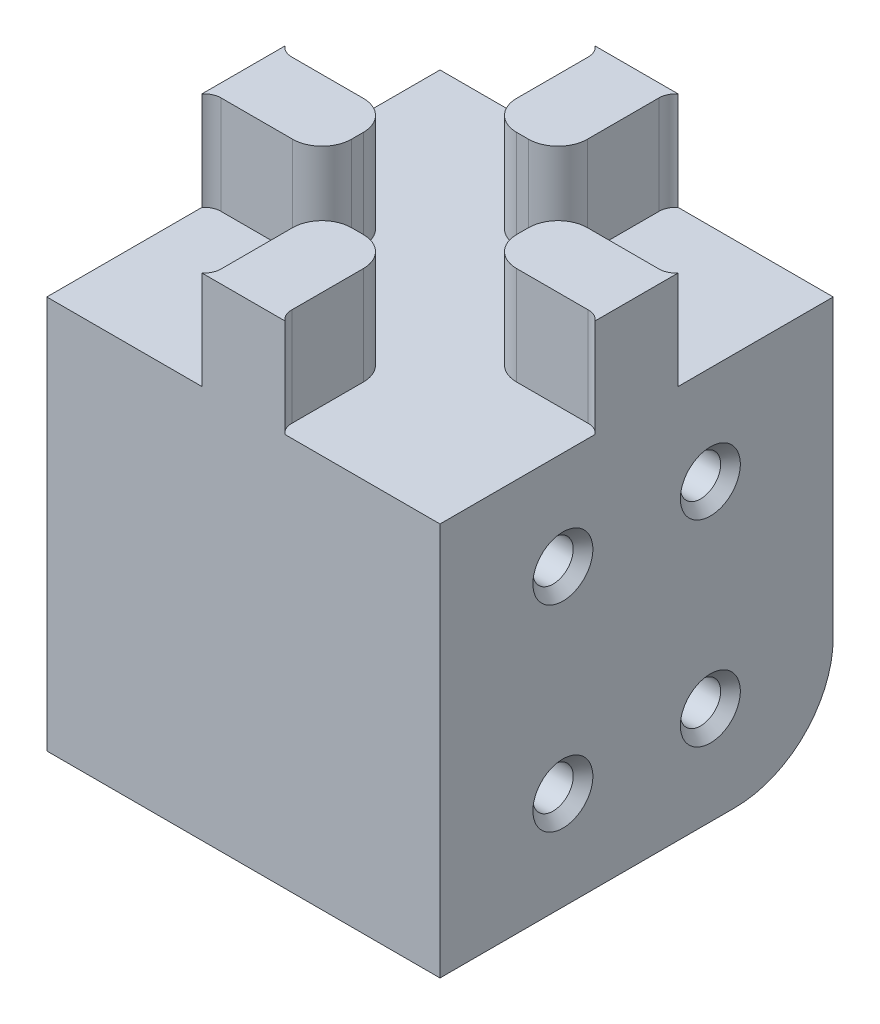
SolidWorks part; units mm, degrees
material "ABS"
ref_plane "Front Plane" through (0, 0, 0) normal (0, 0, 1) x (1, 0, 0)
ref_plane "Top Plane" through (0, 0, 0) normal (0, 1, 0) x (1, 0, 0)
ref_plane "Right Plane" through (0, 0, 0) normal (1, 0, 0) x (0, 0, -1)
sketch "Sketch1" plane through (0, 0, 0) normal (0, 1, 0) x (1, 0, 0)
  line L1 (-20, -20) -> (20, -20)
  line L2 (-20, -20) -> (-20, 20)
  line L3 (-20, 20) -> (20, 20)
  line L4 (20, -20) -> (20, 20)
  line L5 (-20, -20) -> (20, 20) construction
  line L6 (-20, 20) -> (20, -20) construction
  point P0 (0, 0)
  dimension "D1" = 40
  dimension "D2" = 40
extrude "Boss-Extrude1" add sketch "Sketch1" along normal mid plane 40 contours L3 L4 L1 L2
sketch "Sketch2" plane through (0, 0, 0) normal (1, 0, 0) x (0, 0, -1)
  line B0 (-7.5, -10) -> (-7.5, 10) construction
  line B1 (7.5, -10) -> (7.5, 10) construction
  circle B2 centre (-7.5, 10) radius 2.05
  circle B3 centre (7.5, 10) radius 2.05
  circle B4 centre (-7.5, -10) radius 2.05
  circle B5 centre (7.5, -10) radius 2.05
sketch_block_instance "Block1-1"
sketch_block "Block1" parameters "D1"=4.1, "D2"=20, "D3"=15
extrude "Cut-Extrude1" cut sketch "Sketch2" against normal through all from offset 13
mirror "Mirror1" about plane through (0, 0, 0) normal (1, 0, 0) of "Cut-Extrude1"
sketch "Sketch3" plane through (0, 20, 0) normal (0, 1, 0) x (1, 0, 0)
  line L0 (11.8267, 9.3942) -> (11.8267, 9.4899)
  line L1 (11.8267, 9.4899) -> (11.9223, 9.4899)
  line L2 (11.9223, 9.4899) -> (12.39, 9.9576)
  line L3 (12.39, 9.9576) -> (12.39, 10.0532)
  line L4 (12.39, 10.0532) -> (12.4857, 10.0532)
  line L5 (12.4857, 10.0532) -> (12.9739, 10.5414)
  line L6 (13.1153, 10.6) -> (16.76, 10.6)
  line L7 (16.96, 10.4) -> (16.96, 7.15)
  line L8 (16.96, 7.15) -> (16.3, 7.15)
  line L9 (16.3, 7.15) -> (16.3, 5.32)
  line L10 (18.02, 3.6) -> (18.68, 3.6)
  line L11 (20.4, 5.32) -> (20.4, 17)
  line L12 (17, 20.4) -> (5.32, 20.4)
  line L13 (3.6, 18.68) -> (3.6, 18.02)
  line L14 (5.32, 16.3) -> (7.15, 16.3)
  line L15 (7.15, 16.3) -> (7.15, 16.96)
  line L16 (7.15, 16.96) -> (10.4, 16.96)
  line L17 (10.6, 16.76) -> (10.6, 13.1153)
  line L18 (10.5414, 12.9739) -> (6.237, 8.6695)
  line L19 (5.5865, 8.4) -> (-5.5865, 8.4)
  line L20 (-6.237, 8.6695) -> (-10.5414, 12.9739)
  line L21 (-10.6, 13.1153) -> (-10.6, 16.76)
  line L22 (-10.4, 16.96) -> (-7.15, 16.96)
  line L23 (-7.15, 16.96) -> (-7.15, 16.3)
  line L24 (-7.15, 16.3) -> (-5.32, 16.3)
  line L25 (-3.6, 18.02) -> (-3.6, 18.68)
  line L26 (-5.32, 20.4) -> (-17, 20.4)
  line L27 (-20.4, 17) -> (-20.4, 5.32)
  line L28 (-18.68, 3.6) -> (-18.02, 3.6)
  line L29 (-16.3, 5.32) -> (-16.3, 7.15)
  line L30 (-16.3, 7.15) -> (-16.96, 7.15)
  line L31 (-16.96, 7.15) -> (-16.96, 10.4)
  line L32 (-16.76, 10.6) -> (-13.1153, 10.6)
  line L33 (-12.9739, 10.5414) -> (-8.6695, 6.237)
  line L34 (-8.4, 5.5865) -> (-8.4, -5.5865)
  line L35 (-8.6695, -6.237) -> (-12.9739, -10.5414)
  line L36 (-13.1153, -10.6) -> (-16.76, -10.6)
  line L37 (-16.96, -10.4) -> (-16.96, -7.15)
  line L38 (-16.96, -7.15) -> (-16.3, -7.15)
  line L39 (-16.3, -7.15) -> (-16.3, -5.32)
  line L40 (-18.02, -3.6) -> (-18.68, -3.6)
  line L41 (-20.4, -5.32) -> (-20.4, -17)
  line L42 (-17, -20.4) -> (-5.32, -20.4)
  line L43 (-3.6, -18.68) -> (-3.6, -18.02)
  line L44 (-5.32, -16.3) -> (-7.15, -16.3)
  line L45 (-7.15, -16.3) -> (-7.15, -16.96)
  line L46 (-7.15, -16.96) -> (-10.4, -16.96)
  line L47 (-10.6, -16.76) -> (-10.6, -13.1153)
  line L48 (-10.5414, -12.9739) -> (-6.237, -8.6695)
  line L49 (-5.5865, -8.4) -> (5.5865, -8.4)
  line L50 (6.237, -8.6695) -> (10.5414, -12.9739)
  line L51 (10.6, -13.1153) -> (10.6, -16.76)
  line L52 (10.4, -16.96) -> (7.15, -16.96)
  line L53 (7.15, -16.96) -> (7.15, -16.3)
  line L54 (7.15, -16.3) -> (5.32, -16.3)
  line L55 (3.6, -18.02) -> (3.6, -18.68)
  line L56 (5.32, -20.4) -> (17, -20.4)
  line L57 (20.4, -17) -> (20.4, -5.32)
  line L58 (18.68, -3.6) -> (18.02, -3.6)
  line L59 (16.3, -5.32) -> (16.3, -7.15)
  line L60 (16.3, -7.15) -> (16.96, -7.15)
  line L61 (16.96, -7.15) -> (16.96, -10.4)
  line L62 (16.76, -10.6) -> (13.1153, -10.6)
  line L63 (12.9739, -10.5414) -> (8.6695, -6.237)
  line L64 (8.4, -5.5865) -> (8.4, 5.5865)
  line L65 (8.6695, 6.237) -> (11.8267, 9.3942)
  line L66 (11.4267, 9.5599) -> (11.4267, 9.8899)
  line L67 (11.4267, 9.8899) -> (11.7567, 9.8899)
  line L68 (11.7567, 9.8899) -> (11.99, 10.1232)
  line L69 (11.99, 10.1232) -> (11.99, 10.4532)
  line L70 (11.99, 10.4532) -> (12.32, 10.4532)
  line L71 (12.32, 10.4532) -> (12.691, 10.8243)
  line L72 (13.1153, 11) -> (16.76, 11)
  line L73 (17.36, 10.4) -> (17.36, 6.75)
  line L74 (17.36, 6.75) -> (16.7, 6.75)
  line L75 (16.7, 6.75) -> (16.7, 5.32)
  line L76 (18.02, 4) -> (18.68, 4)
  line L77 (20, 5.32) -> (20, 17)
  line L78 (17, 20) -> (5.32, 20)
  line L79 (4, 18.68) -> (4, 18.02)
  line L80 (5.32, 16.7) -> (6.75, 16.7)
  line L81 (6.75, 16.7) -> (6.75, 17.36)
  line L82 (6.75, 17.36) -> (10.4, 17.36)
  line L83 (11, 16.76) -> (11, 13.1153)
  line L84 (10.8243, 12.691) -> (6.5199, 8.3866)
  line L85 (5.5865, 8) -> (-5.5865, 8)
  line L86 (-6.5199, 8.3866) -> (-10.8243, 12.691)
  line L87 (-11, 13.1153) -> (-11, 16.76)
  line L88 (-10.4, 17.36) -> (-6.75, 17.36)
  line L89 (-6.75, 17.36) -> (-6.75, 16.7)
  line L90 (-6.75, 16.7) -> (-5.32, 16.7)
  line L91 (-4, 18.02) -> (-4, 18.68)
  line L92 (-5.32, 20) -> (-17, 20)
  line L93 (-20, 17) -> (-20, 5.32)
  line L94 (-18.68, 4) -> (-18.02, 4)
  line L95 (-16.7, 5.32) -> (-16.7, 6.75)
  line L96 (-16.7, 6.75) -> (-17.36, 6.75)
  line L97 (-17.36, 6.75) -> (-17.36, 10.4)
  line L98 (-16.76, 11) -> (-13.1153, 11)
  line L99 (-12.691, 10.8243) -> (-8.3866, 6.5199)
  line L100 (-8, 5.5865) -> (-8, -5.5865)
  line L101 (-8.3866, -6.5199) -> (-12.691, -10.8243)
  line L102 (-13.1153, -11) -> (-16.76, -11)
  line L103 (-17.36, -10.4) -> (-17.36, -6.75)
  line L104 (-17.36, -6.75) -> (-16.7, -6.75)
  line L105 (-16.7, -6.75) -> (-16.7, -5.32)
  line L106 (-18.02, -4) -> (-18.68, -4)
  line L107 (-20, -5.32) -> (-20, -17)
  line L108 (-17, -20) -> (-5.32, -20)
  line L109 (-4, -18.68) -> (-4, -18.02)
  line L110 (-5.32, -16.7) -> (-6.75, -16.7)
  line L111 (-6.75, -16.7) -> (-6.75, -17.36)
  line L112 (-6.75, -17.36) -> (-10.4, -17.36)
  line L113 (-11, -16.76) -> (-11, -13.1153)
  line L114 (-10.8243, -12.691) -> (-6.5199, -8.3866)
  line L115 (-5.5865, -8) -> (5.5865, -8)
  line L116 (6.5199, -8.3866) -> (10.8243, -12.691)
  line L117 (11, -13.1153) -> (11, -16.76)
  line L118 (10.4, -17.36) -> (6.75, -17.36)
  line L119 (6.75, -17.36) -> (6.75, -16.7)
  line L120 (6.75, -16.7) -> (5.32, -16.7)
  line L121 (4, -18.02) -> (4, -18.68)
  line L122 (5.32, -20) -> (17, -20)
  line L123 (20, -17) -> (20, -5.32)
  line L124 (18.68, -4) -> (18.02, -4)
  line L125 (16.7, -5.32) -> (16.7, -6.75)
  line L126 (16.7, -6.75) -> (17.36, -6.75)
  line L127 (17.36, -6.75) -> (17.36, -10.4)
  line L128 (16.76, -11) -> (13.1153, -11)
  line L129 (12.691, -10.8243) -> (8.3866, -6.5199)
  line L130 (8, -5.5865) -> (8, 5.5865)
  line L131 (8.3866, 6.5199) -> (11.4267, 9.5599)
  line L132 (11.4267, 9.5599) -> (11.4267, 9.8899)
  line L133 (11.4267, 9.8899) -> (11.7567, 9.8899)
  line L134 (11.7567, 9.8899) -> (11.99, 10.1232)
  line L135 (11.99, 10.1232) -> (11.99, 10.4532)
  line L136 (11.99, 10.4532) -> (12.32, 10.4532)
  line L137 (12.32, 10.4532) -> (12.691, 10.8243)
  line L138 (13.1153, 11) -> (16.76, 11)
  line L139 (17.36, 10.4) -> (17.36, 6.75)
  line L140 (17.36, 6.75) -> (16.7, 6.75)
  line L141 (16.7, 6.75) -> (16.7, 5.32)
  line L142 (18.02, 4) -> (18.68, 4)
  line L143 (20, 5.32) -> (20, 17)
  line L144 (17, 20) -> (5.32, 20)
  line L145 (4, 18.68) -> (4, 18.02)
  line L146 (5.32, 16.7) -> (6.75, 16.7)
  line L147 (6.75, 16.7) -> (6.75, 17.36)
  line L148 (6.75, 17.36) -> (10.4, 17.36)
  line L149 (11, 16.76) -> (11, 13.1153)
  line L150 (10.8243, 12.691) -> (6.5199, 8.3866)
  line L151 (5.5865, 8) -> (-5.5865, 8)
  line L152 (-6.5199, 8.3866) -> (-10.8243, 12.691)
  line L153 (-11, 13.1153) -> (-11, 16.76)
  line L154 (-10.4, 17.36) -> (-6.75, 17.36)
  line L155 (-6.75, 17.36) -> (-6.75, 16.7)
  line L156 (-6.75, 16.7) -> (-5.32, 16.7)
  line L157 (-4, 18.02) -> (-4, 18.68)
  line L158 (-5.32, 20) -> (-17, 20)
  line L159 (-20, 17) -> (-20, 5.32)
  line L160 (-18.68, 4) -> (-18.02, 4)
  line L161 (-16.7, 5.32) -> (-16.7, 6.75)
  line L162 (-16.7, 6.75) -> (-17.36, 6.75)
  line L163 (-17.36, 6.75) -> (-17.36, 10.4)
  line L164 (-16.76, 11) -> (-13.1153, 11)
  line L165 (-12.691, 10.8243) -> (-8.3866, 6.5199)
  line L166 (-8, 5.5865) -> (-8, -5.5865)
  line L167 (-8.3866, -6.5199) -> (-12.691, -10.8243)
  line L168 (-13.1153, -11) -> (-16.76, -11)
  line L169 (-17.36, -10.4) -> (-17.36, -6.75)
  line L170 (-17.36, -6.75) -> (-16.7, -6.75)
  line L171 (-16.7, -6.75) -> (-16.7, -5.32)
  line L172 (-18.02, -4) -> (-18.68, -4)
  line L173 (-20, -5.32) -> (-20, -17)
  line L174 (-17, -20) -> (-5.32, -20)
  line L175 (-4, -18.68) -> (-4, -18.02)
  line L176 (-5.32, -16.7) -> (-6.75, -16.7)
  line L177 (-6.75, -16.7) -> (-6.75, -17.36)
  line L178 (-6.75, -17.36) -> (-10.4, -17.36)
  line L179 (-11, -16.76) -> (-11, -13.1153)
  line L180 (-10.8243, -12.691) -> (-6.5199, -8.3866)
  line L181 (-5.5865, -8) -> (5.5865, -8)
  line L182 (6.5199, -8.3866) -> (10.8243, -12.691)
  line L183 (11, -13.1153) -> (11, -16.76)
  line L184 (10.4, -17.36) -> (6.75, -17.36)
  line L185 (6.75, -17.36) -> (6.75, -16.7)
  line L186 (6.75, -16.7) -> (5.32, -16.7)
  line L187 (4, -18.02) -> (4, -18.68)
  line L188 (5.32, -20) -> (17, -20)
  line L189 (20, -17) -> (20, -5.32)
  line L190 (18.68, -4) -> (18.02, -4)
  line L191 (16.7, -5.32) -> (16.7, -6.75)
  line L192 (16.7, -6.75) -> (17.36, -6.75)
  line L193 (17.36, -6.75) -> (17.36, -10.4)
  line L194 (16.76, -11) -> (13.1153, -11)
  line L195 (12.691, -10.8243) -> (8.3866, -6.5199)
  line L196 (8, -5.5865) -> (8, 5.5865)
  line L197 (8.3866, 6.5199) -> (11.4267, 9.5599)
  line L198 (-18.02, 3.6) -> (-8.4, 3.6)
  line L199 (-18.02, -3.6) -> (-8.4, -3.6)
  line L200 (-3.6, -18.02) -> (-3.6, -8.4)
  line L201 (3.6, -18.02) -> (3.6, -8.4)
  line L202 (-20, 20) -> (-20, -20)
  line L203 (-20, -20) -> (20, -20)
  line L204 (20, -20) -> (20, 20)
  line L205 (20, 20) -> (-20, 20)
  line L206 (-20, 20) -> (-20, -20)
  line L207 (-20, -20) -> (20, -20)
  line L208 (20, -20) -> (20, 20)
  line L209 (20, 20) -> (-20, 20)
  line L210 (18.02, 3.6) -> (8.4, 3.6)
  line L211 (18.02, -3.6) -> (8.4, -3.6)
  line L212 (-3.6, 18.02) -> (-3.6, 8)
  line L213 (3.6, 18.02) -> (3.6, 8.4)
  arc A0 (13.1153, 10.6) -> (12.9739, 10.5414) centre (13.1153, 10.4) ccw
  arc A1 (16.96, 10.4) -> (16.76, 10.6) centre (16.76, 10.4) ccw
  arc A2 (16.3, 5.32) -> (18.02, 3.6) centre (18.02, 5.32) ccw
  arc A3 (18.68, 3.6) -> (20.4, 5.32) centre (18.68, 5.32) ccw
  arc A4 (20.4, 17) -> (17, 20.4) centre (17, 17) ccw
  arc A5 (5.32, 20.4) -> (3.6, 18.68) centre (5.32, 18.68) ccw
  arc A6 (3.6, 18.02) -> (5.32, 16.3) centre (5.32, 18.02) ccw
  arc A7 (10.6, 16.76) -> (10.4, 16.96) centre (10.4, 16.76) ccw
  arc A8 (10.5414, 12.9739) -> (10.6, 13.1153) centre (10.4, 13.1153) ccw
  arc A9 (5.5865, 8.4) -> (6.237, 8.6695) centre (5.5865, 9.32) ccw
  arc A10 (-6.237, 8.6695) -> (-5.5865, 8.4) centre (-5.5865, 9.32) ccw
  arc A11 (-10.6, 13.1153) -> (-10.5414, 12.9739) centre (-10.4, 13.1153) ccw
  arc A12 (-10.4, 16.96) -> (-10.6, 16.76) centre (-10.4, 16.76) ccw
  arc A13 (-5.32, 16.3) -> (-3.6, 18.02) centre (-5.32, 18.02) ccw
  arc A14 (-3.6, 18.68) -> (-5.32, 20.4) centre (-5.32, 18.68) ccw
  arc A15 (-17, 20.4) -> (-20.4, 17) centre (-17, 17) ccw
  arc A16 (-20.4, 5.32) -> (-18.68, 3.6) centre (-18.68, 5.32) ccw
  arc A17 (-18.02, 3.6) -> (-16.3, 5.32) centre (-18.02, 5.32) ccw
  arc A18 (-16.76, 10.6) -> (-16.96, 10.4) centre (-16.76, 10.4) ccw
  arc A19 (-12.9739, 10.5414) -> (-13.1153, 10.6) centre (-13.1153, 10.4) ccw
  arc A20 (-8.4, 5.5865) -> (-8.6695, 6.237) centre (-9.32, 5.5865) ccw
  arc A21 (-8.6695, -6.237) -> (-8.4, -5.5865) centre (-9.32, -5.5865) ccw
  arc A22 (-13.1153, -10.6) -> (-12.9739, -10.5414) centre (-13.1153, -10.4) ccw
  arc A23 (-16.96, -10.4) -> (-16.76, -10.6) centre (-16.76, -10.4) ccw
  arc A24 (-16.3, -5.32) -> (-18.02, -3.6) centre (-18.02, -5.32) ccw
  arc A25 (-18.68, -3.6) -> (-20.4, -5.32) centre (-18.68, -5.32) ccw
  arc A26 (-20.4, -17) -> (-17, -20.4) centre (-17, -17) ccw
  arc A27 (-5.32, -20.4) -> (-3.6, -18.68) centre (-5.32, -18.68) ccw
  arc A28 (-3.6, -18.02) -> (-5.32, -16.3) centre (-5.32, -18.02) ccw
  arc A29 (-10.6, -16.76) -> (-10.4, -16.96) centre (-10.4, -16.76) ccw
  arc A30 (-10.5414, -12.9739) -> (-10.6, -13.1153) centre (-10.4, -13.1153) ccw
  arc A31 (-5.5865, -8.4) -> (-6.237, -8.6695) centre (-5.5865, -9.32) ccw
  arc A32 (6.237, -8.6695) -> (5.5865, -8.4) centre (5.5865, -9.32) ccw
  arc A33 (10.6, -13.1153) -> (10.5414, -12.9739) centre (10.4, -13.1153) ccw
  arc A34 (10.4, -16.96) -> (10.6, -16.76) centre (10.4, -16.76) ccw
  arc A35 (5.32, -16.3) -> (3.6, -18.02) centre (5.32, -18.02) ccw
  arc A36 (3.6, -18.68) -> (5.32, -20.4) centre (5.32, -18.68) ccw
  arc A37 (17, -20.4) -> (20.4, -17) centre (17, -17) ccw
  arc A38 (20.4, -5.32) -> (18.68, -3.6) centre (18.68, -5.32) ccw
  arc A39 (18.02, -3.6) -> (16.3, -5.32) centre (18.02, -5.32) ccw
  arc A40 (16.76, -10.6) -> (16.96, -10.4) centre (16.76, -10.4) ccw
  arc A41 (12.9739, -10.5414) -> (13.1153, -10.6) centre (13.1153, -10.4) ccw
  arc A42 (8.4, -5.5865) -> (8.6695, -6.237) centre (9.32, -5.5865) ccw
  arc A43 (8.6695, 6.237) -> (8.4, 5.5865) centre (9.32, 5.5865) ccw
  arc A44 (13.1153, 11) -> (12.691, 10.8243) centre (13.1153, 10.4) ccw
  arc A45 (17.36, 10.4) -> (16.76, 11) centre (16.76, 10.4) ccw
  arc A46 (16.7, 5.32) -> (18.02, 4) centre (18.02, 5.32) ccw
  arc A47 (18.68, 4) -> (20, 5.32) centre (18.68, 5.32) ccw
  arc A48 (20, 17) -> (17, 20) centre (17, 17) ccw
  arc A49 (5.32, 20) -> (4, 18.68) centre (5.32, 18.68) ccw
  arc A50 (4, 18.02) -> (5.32, 16.7) centre (5.32, 18.02) ccw
  arc A51 (11, 16.76) -> (10.4, 17.36) centre (10.4, 16.76) ccw
  arc A52 (10.8243, 12.691) -> (11, 13.1153) centre (10.4, 13.1153) ccw
  arc A53 (5.5865, 8) -> (6.5199, 8.3866) centre (5.5865, 9.32) ccw
  arc A54 (-6.5199, 8.3866) -> (-5.5865, 8) centre (-5.5865, 9.32) ccw
  arc A55 (-11, 13.1153) -> (-10.8243, 12.691) centre (-10.4, 13.1153) ccw
  arc A56 (-10.4, 17.36) -> (-11, 16.76) centre (-10.4, 16.76) ccw
  arc A57 (-5.32, 16.7) -> (-4, 18.02) centre (-5.32, 18.02) ccw
  arc A58 (-4, 18.68) -> (-5.32, 20) centre (-5.32, 18.68) ccw
  arc A59 (-17, 20) -> (-20, 17) centre (-17, 17) ccw
  arc A60 (-20, 5.32) -> (-18.68, 4) centre (-18.68, 5.32) ccw
  arc A61 (-18.02, 4) -> (-16.7, 5.32) centre (-18.02, 5.32) ccw
  arc A62 (-16.76, 11) -> (-17.36, 10.4) centre (-16.76, 10.4) ccw
  arc A63 (-12.691, 10.8243) -> (-13.1153, 11) centre (-13.1153, 10.4) ccw
  arc A64 (-8, 5.5865) -> (-8.3866, 6.5199) centre (-9.32, 5.5865) ccw
  arc A65 (-8.3866, -6.5199) -> (-8, -5.5865) centre (-9.32, -5.5865) ccw
  arc A66 (-13.1153, -11) -> (-12.691, -10.8243) centre (-13.1153, -10.4) ccw
  arc A67 (-17.36, -10.4) -> (-16.76, -11) centre (-16.76, -10.4) ccw
  arc A68 (-16.7, -5.32) -> (-18.02, -4) centre (-18.02, -5.32) ccw
  arc A69 (-18.68, -4) -> (-20, -5.32) centre (-18.68, -5.32) ccw
  arc A70 (-20, -17) -> (-17, -20) centre (-17, -17) ccw
  arc A71 (-5.32, -20) -> (-4, -18.68) centre (-5.32, -18.68) ccw
  arc A72 (-4, -18.02) -> (-5.32, -16.7) centre (-5.32, -18.02) ccw
  arc A73 (-11, -16.76) -> (-10.4, -17.36) centre (-10.4, -16.76) ccw
  arc A74 (-10.8243, -12.691) -> (-11, -13.1153) centre (-10.4, -13.1153) ccw
  arc A75 (-5.5865, -8) -> (-6.5199, -8.3866) centre (-5.5865, -9.32) ccw
  arc A76 (6.5199, -8.3866) -> (5.5865, -8) centre (5.5865, -9.32) ccw
  arc A77 (11, -13.1153) -> (10.8243, -12.691) centre (10.4, -13.1153) ccw
  arc A78 (10.4, -17.36) -> (11, -16.76) centre (10.4, -16.76) ccw
  arc A79 (5.32, -16.7) -> (4, -18.02) centre (5.32, -18.02) ccw
  arc A80 (4, -18.68) -> (5.32, -20) centre (5.32, -18.68) ccw
  arc A81 (17, -20) -> (20, -17) centre (17, -17) ccw
  arc A82 (20, -5.32) -> (18.68, -4) centre (18.68, -5.32) ccw
  arc A83 (18.02, -4) -> (16.7, -5.32) centre (18.02, -5.32) ccw
  arc A84 (16.76, -11) -> (17.36, -10.4) centre (16.76, -10.4) ccw
  arc A85 (12.691, -10.8243) -> (13.1153, -11) centre (13.1153, -10.4) ccw
  arc A86 (8, -5.5865) -> (8.3866, -6.5199) centre (9.32, -5.5865) ccw
  arc A87 (8.3866, 6.5199) -> (8, 5.5865) centre (9.32, 5.5865) ccw
  arc A88 (13.1153, 11) -> (12.691, 10.8243) centre (13.1153, 10.4) ccw
  arc A89 (17.36, 10.4) -> (16.76, 11) centre (16.76, 10.4) ccw
  arc A90 (16.7, 5.32) -> (18.02, 4) centre (18.02, 5.32) ccw
  arc A91 (18.68, 4) -> (20, 5.32) centre (18.68, 5.32) ccw
  arc A92 (20, 17) -> (17, 20) centre (17, 17) ccw
  arc A93 (5.32, 20) -> (4, 18.68) centre (5.32, 18.68) ccw
  arc A94 (4, 18.02) -> (5.32, 16.7) centre (5.32, 18.02) ccw
  arc A95 (11, 16.76) -> (10.4, 17.36) centre (10.4, 16.76) ccw
  arc A96 (10.8243, 12.691) -> (11, 13.1153) centre (10.4, 13.1153) ccw
  arc A97 (5.5865, 8) -> (6.5199, 8.3866) centre (5.5865, 9.32) ccw
  arc A98 (-6.5199, 8.3866) -> (-5.5865, 8) centre (-5.5865, 9.32) ccw
  arc A99 (-11, 13.1153) -> (-10.8243, 12.691) centre (-10.4, 13.1153) ccw
  arc A100 (-10.4, 17.36) -> (-11, 16.76) centre (-10.4, 16.76) ccw
  arc A101 (-5.32, 16.7) -> (-4, 18.02) centre (-5.32, 18.02) ccw
  arc A102 (-4, 18.68) -> (-5.32, 20) centre (-5.32, 18.68) ccw
  arc A103 (-17, 20) -> (-20, 17) centre (-17, 17) ccw
  arc A104 (-20, 5.32) -> (-18.68, 4) centre (-18.68, 5.32) ccw
  arc A105 (-18.02, 4) -> (-16.7, 5.32) centre (-18.02, 5.32) ccw
  arc A106 (-16.76, 11) -> (-17.36, 10.4) centre (-16.76, 10.4) ccw
  arc A107 (-12.691, 10.8243) -> (-13.1153, 11) centre (-13.1153, 10.4) ccw
  arc A108 (-8, 5.5865) -> (-8.3866, 6.5199) centre (-9.32, 5.5865) ccw
  arc A109 (-8.3866, -6.5199) -> (-8, -5.5865) centre (-9.32, -5.5865) ccw
  arc A110 (-13.1153, -11) -> (-12.691, -10.8243) centre (-13.1153, -10.4) ccw
  arc A111 (-17.36, -10.4) -> (-16.76, -11) centre (-16.76, -10.4) ccw
  arc A112 (-16.7, -5.32) -> (-18.02, -4) centre (-18.02, -5.32) ccw
  arc A113 (-18.68, -4) -> (-20, -5.32) centre (-18.68, -5.32) ccw
  arc A114 (-20, -17) -> (-17, -20) centre (-17, -17) ccw
  arc A115 (-5.32, -20) -> (-4, -18.68) centre (-5.32, -18.68) ccw
  arc A116 (-4, -18.02) -> (-5.32, -16.7) centre (-5.32, -18.02) ccw
  arc A117 (-11, -16.76) -> (-10.4, -17.36) centre (-10.4, -16.76) ccw
  arc A118 (-10.8243, -12.691) -> (-11, -13.1153) centre (-10.4, -13.1153) ccw
  arc A119 (-5.5865, -8) -> (-6.5199, -8.3866) centre (-5.5865, -9.32) ccw
  arc A120 (6.5199, -8.3866) -> (5.5865, -8) centre (5.5865, -9.32) ccw
  arc A121 (11, -13.1153) -> (10.8243, -12.691) centre (10.4, -13.1153) ccw
  arc A122 (10.4, -17.36) -> (11, -16.76) centre (10.4, -16.76) ccw
  arc A123 (5.32, -16.7) -> (4, -18.02) centre (5.32, -18.02) ccw
  arc A124 (4, -18.68) -> (5.32, -20) centre (5.32, -18.68) ccw
  arc A125 (17, -20) -> (20, -17) centre (17, -17) ccw
  arc A126 (20, -5.32) -> (18.68, -4) centre (18.68, -5.32) ccw
  arc A127 (18.02, -4) -> (16.7, -5.32) centre (18.02, -5.32) ccw
  arc A128 (16.76, -11) -> (17.36, -10.4) centre (16.76, -10.4) ccw
  arc A129 (12.691, -10.8243) -> (13.1153, -11) centre (13.1153, -10.4) ccw
  arc A130 (8, -5.5865) -> (8.3866, -6.5199) centre (9.32, -5.5865) ccw
  arc A131 (8.3866, 6.5199) -> (8, 5.5865) centre (9.32, 5.5865) ccw
  dimension "D1" = 0
  dimension "D2" = 0.4
  dimension "D3" = 0
extrude "Boss-Extrude2" add sketch "Sketch3" along normal blind 10 contours A25 L40 A24 L39 L38 L37 A23 L36 A22 L35 A21 L34 A20 L33 A19 L32 A18 L31 L30 L29 A17 L28 A16 L206 | A14 L25 A13 L24 L23 L22 A12 L21 A11 L20 A10 L19 A9 L18 A8 L17 A7 L16 L15 L14 A6 L13 A5 L209 | A36 L55 L201 L49 L200 L43 A27 L207 | A38 L208 A3 L10 L210 L64 L211 L58
fillet "Fillet1" radius 10 1 edges at (0, -20, -20)
chamfer "Chamfer1" distance 1 angle 45 8 edges at (20, 10, 5.45) (20, -10, 5.45) (20, 10, -9.55) (20, -10, -9.55) (-20, -10, 5.45) (-20, 10, 5.45) (-20, 10, -9.55) (-20, -10, -9.55)
fillet "Fillet2" radius 3 8 edges at (-3.6, 25, 8.4) (8.4, 25, -3.6) (8.4, 25, 3.6) (3.6, 25, 8.4) (-3.6, 25, -8.4) (-8.4, 25, 3.6) (-8.4, 25, -3.6) (3.6, 25, -8.4)
